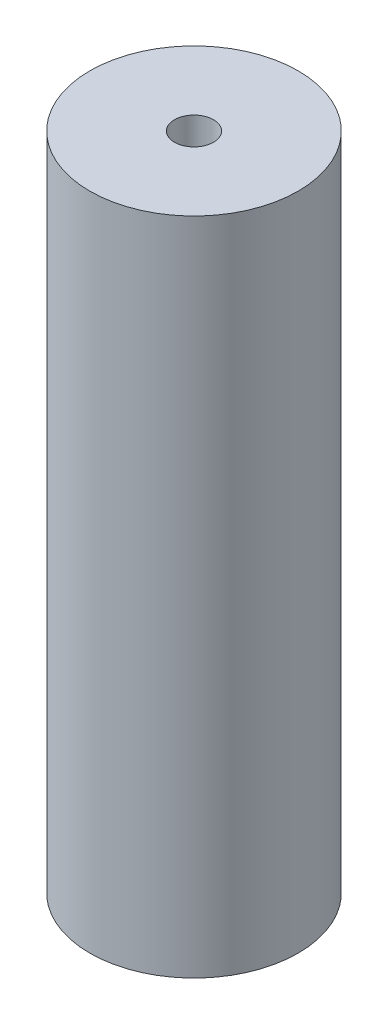
SolidWorks part; units mm, degrees
ref_plane "Ebene vorne" through (0, 0, 0) normal (0, 0, 1) x (1, 0, 0)
ref_plane "Ebene oben" through (0, 0, 0) normal (0, 1, 0) x (1, 0, 0)
ref_plane "Ebene rechts" through (0, 0, 0) normal (1, 0, 0) x (0, 0, -1)
sketch "Skizze1" plane through (0, 0, 0) normal (0, 1, 0) x (1, 0, 0)
  circle A0 centre (0, 0) radius 6
  dimension "D1" = 12
extrude "Aufsatz-Linear austragen1" add sketch "Skizze1" along normal blind 38
sketch "Skizze2" plane through (0, 0, 0) normal (0, -1, 0) x (-1, 0, 0)
  circle A0 centre (0, 0) radius 1.125
  dimension "D1" = 2.25
extrude "Schnitt-Linear austragen1" cut sketch "Skizze2" against normal through all
sketch "Skizze3" plane through (0, 0, 0) normal (0, -1, 0) x (-1, 0, 0)
  circle A0 centre (0, 0) radius 2.75
  dimension "D1" = 5.5
extrude "Schnitt-Linear austragen2" cut sketch "Skizze3" against normal offset from surface (21 mm away) 17 up to face at (0, 38, -1.125)
